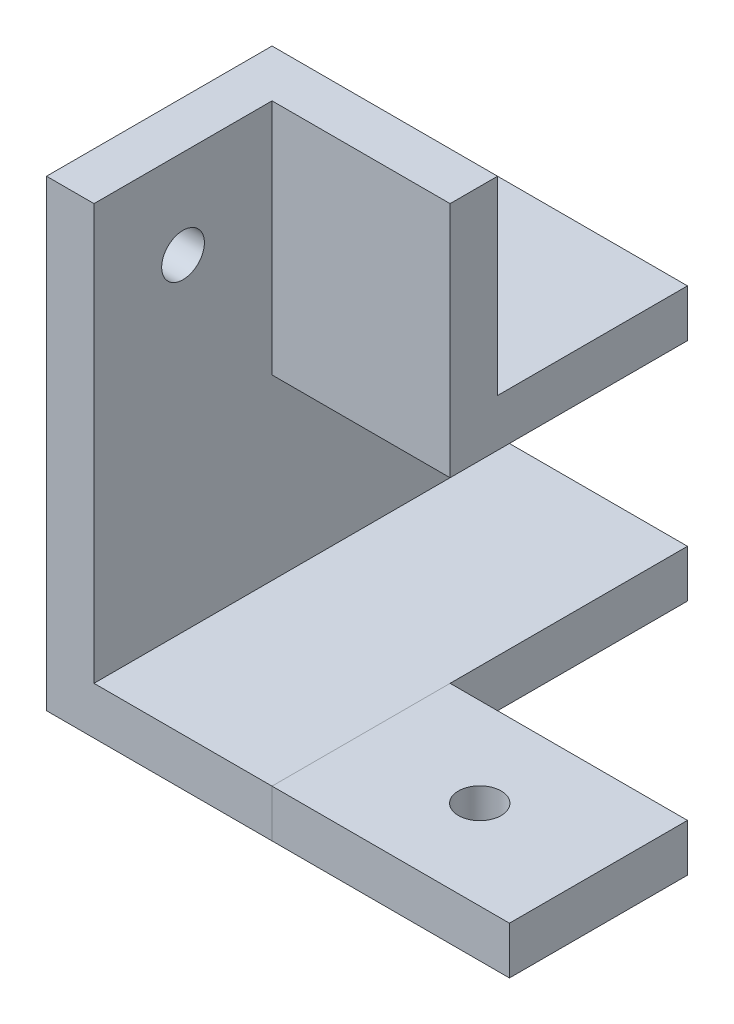
SolidWorks part; units mm, degrees
ref_plane "前视基准面" through (0, 0, 0) normal (0, 0, 1) x (1, 0, 0)
ref_plane "上视基准面" through (0, 0, 0) normal (0, 1, 0) x (1, 0, 0)
ref_plane "右视基准面" through (0, 0, 0) normal (1, 0, 0) x (0, 0, -1)
sketch "草图1" plane through (0, 0, 0) normal (0, 0, 1) x (1, 0, 0)
  line L1 (-4, 19) -> (0, 19)
  line L2 (-4, 19) -> (-4, 0)
  line L3 (-4, 0) -> (0, 0)
  line L4 (0, 19) -> (0, 0)
  line L5 (0, 0) -> (15, 0)
  line L6 (0, 0) -> (0, 4)
  line L7 (0, 4) -> (15, 4)
  line L8 (15, 0) -> (15, 4)
  dimension "D1" = 4
  dimension "D2" = 4
  dimension "D3" = 15
  dimension "D4" = 15
extrude "凸台-拉伸1" add sketch "草图1" along normal blind 15 contours L4 L1 L2 L3 | L5 L8 L7 L4
sketch "草图2" plane through (0, 0, 15) normal (0, 0, 1) x (1, 0, 0)
  line L1 (-4, 19) -> (15, 19)
  line L2 (-4, 19) -> (-4, 0)
  line L3 (-4, 0) -> (15, 0)
  line L4 (15, 19) -> (15, 0)
extrude "凸台-拉伸2" add sketch "草图2" along normal blind 4
sketch "草图3" plane through (0, 0, 0) normal (0, 0, -1) x (-1, 0, 0)
  line L1 (0, 19) -> (4, 19)
  line L2 (0, 19) -> (0, 0)
  line L3 (0, 0) -> (4, 0)
  line L4 (4, 19) -> (4, 0)
  line L5 (0, 0) -> (-15, 0)
  line L6 (0, 0) -> (0, 4)
  line L7 (0, 4) -> (-15, 4)
  line L8 (-15, 0) -> (-15, 4)
  line L13 (4, 19) -> (-15, 19)
  line L14 (4, 19) -> (4, 23)
  line L15 (4, 23) -> (-15, 23)
  line L16 (-15, 19) -> (-15, 23)
  dimension "D1" = 4
extrude "凸台-拉伸3" add sketch "草图3" along normal blind 20
sketch "草图5" plane through (15, 0, 0) normal (1, 0, 0) x (0, 0, -1)
  line L0 (-15, 4) -> (20, 4) construction
  line L1 (-19, 0) -> (-15, 0)
  line L2 (-19, 0) -> (-19, 19)
  line L3 (-19, 19) -> (-15, 19)
  line L4 (-15, 4) -> (-15, 19)
  line L5 (-15, 0) -> (0, 0)
  line L7 (-15, 4) -> (0, 4)
  line L10 (0, 0) -> (4, 0)
  line L11 (0, 4) -> (0, 18)
  line L12 (0, 18) -> (4, 18)
  line L13 (4, 0) -> (4, 18)
  line M3 (-19, 0) -> (20, 0)
  line M5 (20, 4) -> (-15, 4)
  line M6 (-15, 4) -> (-15, 19)
  line M7 (-15, 19) -> (-19, 19)
  line M8 (-19, 19) -> (-19, 0)
  dimension "D1" = 15
  dimension "D2" = 4
extrude "凸台-拉伸5" add sketch "草图5" along normal blind 20 separate body contours L4 M3 M6 M7 M8 | L13 L12 L11 M5
sketch "草图6" plane through (0, 19, 0) normal (0, 1, 0) x (1, 0, 0)
  line L0 (-4, -19) -> (-4, 0) construction
  line L1 (15, -19) -> (-4, -19)
  line L2 (15, -19) -> (15, -15)
  line L3 (15, -15) -> (0, -15)
  line L4 (-4, -19) -> (-4, -16)
  line L7 (-4, -16) -> (-4, 0)
  line L9 (0, -15) -> (0, 0)
  line L10 (-4, 0) -> (0, 0)
  line L14 (15, 3) -> (15, 0)
  line L15 (-4, 0) -> (0, 0) construction
  dimension "D1" = 3
extrude "凸台-拉伸6" add sketch "草图6" along normal blind 20 separate body
sketch "草图7" plane through (0, 23, 0) normal (0, 1, 0) x (1, 0, 0)
  line L0 (15, 20) -> (15, 0) construction
  line L1 (-4, 0) -> (15, 0)
  line L2 (-4, 0) -> (-4, 4)
  line L3 (-4, 4) -> (15, 4)
  line L4 (15, 0) -> (15, 4)
  dimension "D1" = 4
  dimension "D2" = 0
extrude "凸台-拉伸7" add sketch "草图7" along normal blind 16
sketch "草图8" plane through (-4, 0, 0) normal (-1, 0, 0) x (0, 0, 1)
  line L0 (-4, 39) -> (19, 39) construction
  line L1 (-20, 0) -> (-20, 23) construction
  circle A0 centre (7.5, 31.5) radius 1.8
  circle A1 centre (-12.5, 10.5) radius 1.8
  dimension "D2" = 3.6
  dimension "D3" = 7.5
  dimension "D4" = 3.6
  dimension "D1" = 7.5
extrude "切除-拉伸1" cut sketch "草图8" against normal blind 12
sketch "草图9" plane through (0, 0, 0) normal (0, -1, 0) x (1, 0, 0)
  line L0 (35, 19) -> (35, -4) construction
  line L1 (35, 19) -> (15, 19) construction
  circle A0 centre (25, 7.5) radius 1.8
  dimension "D1" = 3.6
  dimension "D3" = 11.5
  dimension "D2" = 10
extrude "切除-拉伸2" cut sketch "草图9" against normal blind 12
sketch "Sketch1" plane through (35, 0, 0) normal (1, 0, 0) x (0, 0, -1)
  line L0 (-19, 19) -> (-15, 19)
  line L1 (-15, 19) -> (-15, 4)
  line L3 (-15, 4) -> (20, 4) construction
  line L4 (0, 4) -> (0, 18)
  line L5 (0, 4) -> (0, 18) construction
  line L6 (0, 18) -> (4.0105, 18)
  line L7 (4.0105, 18) -> (4.0105, 4)
  line L11 (-19, 4) -> (-19, 19)
  line L12 (-19, 4) -> (-15, 4)
  line L13 (0, 4) -> (4.0105, 4)
extrude "Cut-Extrude2" cut sketch "Sketch1" against normal blind 20
sketch "Sketch2" plane through (35, 0, 0) normal (1, 0, 0) x (0, 0, -1)
  line L0 (0, 4) -> (4, 4)
  line L1 (4, 4) -> (-19, 4) construction
  line L2 (0, 4) -> (0, 0)
  line L3 (4, 4) -> (4, 0)
  line L4 (-19, 0) -> (4, 0) construction
  line L5 (4, 0) -> (4, 4) construction
  line L6 (4, 0) -> (0, 0)
extrude "Cut-Extrude3" cut sketch "Sketch2" against normal blind 20
sketch "Sketch3" plane through (0, 0, 19) normal (0, 0, 1) x (1, 0, 0)
  line L0 (-4, 39) -> (15, 39)
  line L1 (15, 39) -> (15, 4)
  line L2 (15, 4) -> (35, 4)
  line L3 (35, 4) -> (35, 0)
  line L4 (35, 0) -> (15, 0) construction
  line L5 (35, 4) -> (35, 0) construction
  line L6 (35, 0) -> (-4, 0)
  line L7 (-4, 0) -> (-4, 39)
extrude "Cut-Extrude4" cut sketch "Sketch3" against normal blind 4
